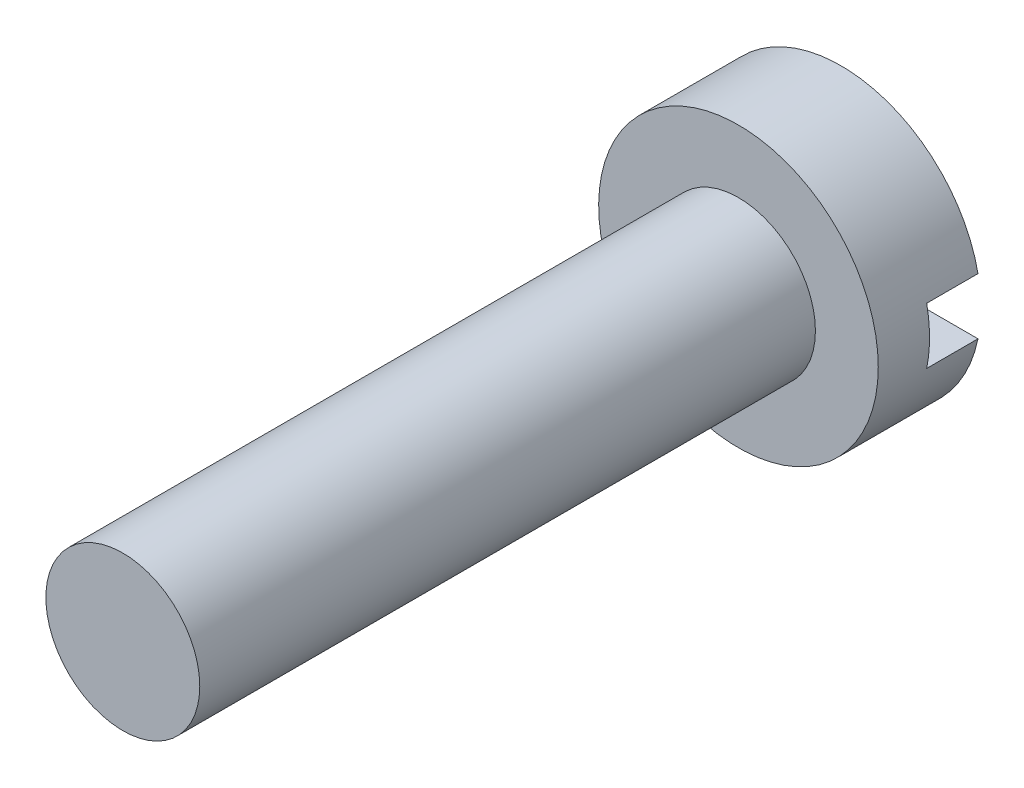
SolidWorks part; units mm, degrees
ref_plane "Front Plane" through (0, 0, 0) normal (0, 0, 1) x (1, 0, 0)
ref_plane "Top Plane" through (0, 0, 0) normal (0, 1, 0) x (1, 0, 0)
ref_plane "Right Plane" through (0, 0, 0) normal (1, 0, 0) x (0, 0, -1)
sketch "Sketch1" plane through (0, 0, 0) normal (0, 0, 1) x (1, 0, 0)
  circle A0 centre (0, 0) radius 2.725
extrude "Extrude1" add sketch "Sketch1" along normal blind 2
sketch "Sketch2" plane through (0, 0, 0) normal (0, 0, -1) x (-1, 0, 0)
  line L0 (-3.9013, 0) -> (3.4498, 0) construction
  line L1 (3.4498, 0) -> (3.4498, 0.55)
  line L2 (3.4498, 0.55) -> (-3.9013, 0.55)
  line L3 (-3.9013, 0.55) -> (-3.9013, -0.55)
  line L4 (-3.9013, -0.55) -> (3.4498, -0.55)
  line L5 (3.4498, -0.55) -> (3.4498, 0)
extrude "Cut-Extrude1" cut sketch "Sketch2" against normal blind 1
sketch "Sketch3" plane through (0, 0, 2) normal (0, 0, 1) x (1, 0, 0)
  circle A0 centre (0, 0) radius 1.5
extrude "Extrude2" add sketch "Sketch3" along normal blind 12
